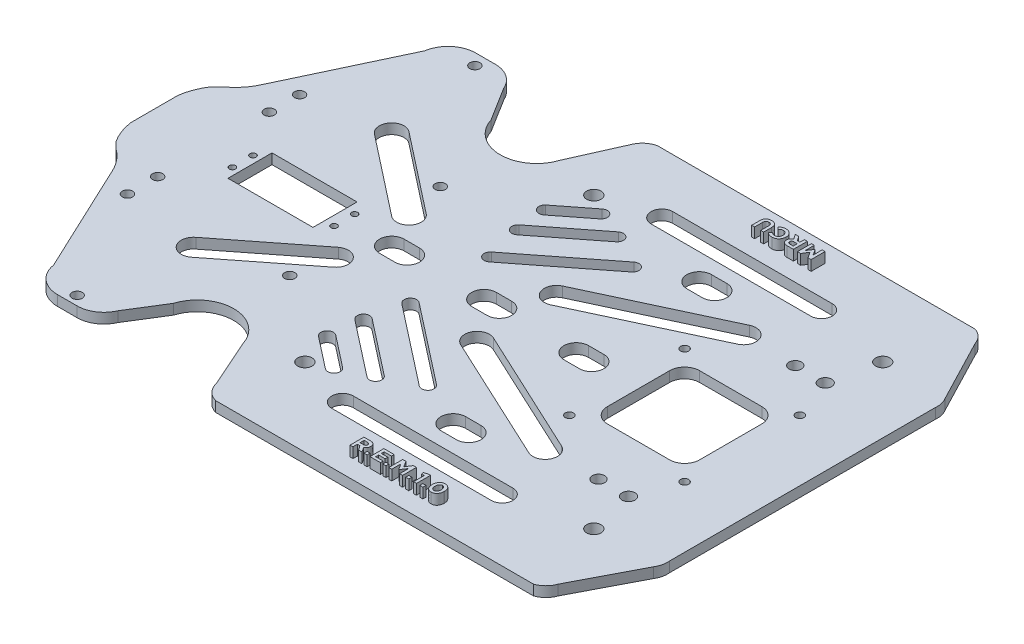
SolidWorks part; units mm, degrees
ref_plane "Front Plane" through (0, 0, 0) normal (0, 0, 1) x (1, 0, 0)
ref_plane "Top Plane" through (0, 0, 0) normal (0, 1, 0) x (1, 0, 0)
ref_plane "Right Plane" through (0, 0, 0) normal (1, 0, 0) x (0, 0, -1)
sketch "Sketch1" plane through (0, 0, 0) normal (0, 1, 0) x (1, 0, 0)
  line L0 (-1500, -0.0781) -> (73500, -0.0781) construction
  line L1 (0, -1000) -> (0, 49000) construction
  line L2 (-150.6518, 26.4257) -> (-153.2975, 23.78)
  line L3 (-157.8453, 11.7876) -> (-157.8453, -10.8775)
  line L4 (-153.2975, -22.8699) -> (-150.6518, -25.5156)
  line L5 (-141.6391, -36.6462) -> (-116.4734, -90.1233)
  line L6 (-103.0506, -101.6219) -> (-93.4928, -101.6219)
  line L7 (-81.4838, -93.7237) -> (-71.0922, -77.0457)
  line L8 (-37.1279, -77.0457) -> (-26.688, -100.4727)
  line L9 (-19.6582, -107.8431) -> (135.4161, -107.8431)
  line L10 (141.4748, -101.8033) -> (157.3462, -71.2851)
  line L11 (158.8522, -64.9974) -> (158.8522, 64.8401)
  line L12 (157.3462, 71.1278) -> (141.4748, 101.646)
  line L13 (135.4161, 107.6858) -> (-19.6582, 107.6858)
  line L14 (-26.688, 101.3828) -> (-37.1279, 77.9558)
  line L15 (-71.0922, 77.9558) -> (-81.4838, 94.6338)
  line L16 (-93.4928, 102.532) -> (-103.0506, 102.532)
  line L17 (-116.4734, 91.0334) -> (-141.6391, 37.5563)
  line L22 (89.8093, 83.5697) -> (11.952, 83.5697)
  line L23 (11.952, 73.0697) -> (89.8093, 73.0697)
  line L24 (-6.436, 67.3784) -> (-21.8022, 55.373)
  line L25 (-18.1047, 50.6541) -> (-2.7385, 62.6595)
  line L26 (7.281, 61.7122) -> (-19.9054, 40.4718)
  line L27 (-16.2114, 35.7438) -> (10.9749, 56.9841)
  line L28 (23.8112, 52.7364) -> (-15.1953, 22.2612)
  line L29 (-11.5014, 17.5331) -> (27.5052, 48.0084)
  line L30 (78.8024, 54.2755) -> (16.5469, 25.2452)
  line L31 (21.6183, 14.3695) -> (83.8738, 43.3998)
  line L32 (48.0667, 54.3972) -> (55.5667, 54.3972)
  line L33 (55.5667, 66.3972) -> (48.0667, 66.3972)
  line L34 (-86.0607, -53.0617) -> (-47.0999, -22.5281)
  line L35 (-54.5037, -13.0876) -> (-93.4646, -43.6212)
  line L36 (48.0667, -5.6028) -> (55.5667, -5.6028)
  line L37 (55.5667, 6.3972) -> (48.0667, 6.3972)
  line L38 (3.0667, -5.6028) -> (10.5667, -5.6028)
  line L39 (10.5667, 6.3972) -> (3.0667, 6.3972)
  line L40 (-41.9333, -5.6028) -> (-34.4333, -5.6028)
  line L41 (-34.4333, 6.3972) -> (-41.9333, 6.3972)
  line L44 (-19.9054, -39.6775) -> (7.281, -60.9178)
  line L45 (10.9749, -56.1898) -> (-16.2114, -34.9494)
  line L46 (-15.1953, -21.4669) -> (23.8112, -51.9421)
  line L47 (27.5052, -47.214) -> (-11.5014, -16.7388)
  line L48 (48.0667, -65.6028) -> (55.5667, -65.6028)
  line L49 (55.5667, -53.6028) -> (48.0667, -53.6028)
  line L50 (11.952, -82.7753) -> (89.8093, -82.7753)
  line L51 (89.8093, -72.2753) -> (11.952, -72.2753)
  line L52 (116.134, 22.8972) -> (85.7494, 22.8972)
  line L53 (123.4417, -14.7951) -> (123.4417, 15.5895)
  line L54 (85.7494, -22.1028) -> (116.134, -22.1028)
  line L55 (78.4417, 15.5895) -> (78.4417, -14.7951)
  line L56 (16.5469, -24.4509) -> (78.8024, -53.4811)
  line L57 (83.8738, -42.6055) -> (21.6183, -13.5752)
  line L58 (-86.0607, 52.9054) -> (-47.0999, 22.3718)
  line L59 (-54.5037, 12.9314) -> (-93.4646, 43.465)
  line L60 (-1118.8056, -0.1232) -> (48881.1944, -0.1232) construction
  line L61 (-118.8056, -1000.1232) -> (-118.8056, 48999.8768) construction
  line L84 (-18.1047, -50.8104) -> (-2.7385, -62.8158)
  line L85 (-6.436, -67.5347) -> (-21.8022, -55.5293)
  line L86 (-89.8594, 22.1796) -> (-89.8594, -22.3358) construction
  line L87 (-69.1094, 10.6107) -> (-110.6094, 10.6107)
  line L88 (-69.1094, -10.8893) -> (-69.1094, 10.6107)
  line L89 (-110.6094, -10.8893) -> (-69.1094, -10.8893)
  line L90 (-110.6094, 10.6107) -> (-110.6094, -10.8893)
  arc A0 (-150.6518, 26.4257) -> (-141.6391, 37.5563) centre (-165.7222, 47.8428) ccw
  arc A1 (-153.2975, 23.78) -> (-157.8453, 11.7876) centre (-131.0414, 8.4816) ccw
  arc A2 (-157.8453, -10.8775) -> (-153.2975, -22.8699) centre (-131.0414, -7.5716) ccw
  arc A3 (-141.6391, -36.6462) -> (-150.6518, -25.5156) centre (-165.7222, -46.9327) ccw
  arc A4 (-116.4734, -90.1233) -> (-103.0506, -101.6219) centre (-103.0506, -88.0381) ccw
  arc A5 (-93.4928, -101.6219) -> (-81.4838, -93.7237) centre (-93.4928, -88.5431) ccw
  arc A6 (-37.1279, -77.0457) -> (-71.0922, -77.0457) centre (-54.11, -82.3517) ccw
  arc A7 (-26.688, -100.4727) -> (-19.6582, -107.8431) centre (-17.0448, -98.3129) ccw
  arc A8 (135.4161, -107.8431) -> (141.4748, -101.8033) centre (132.2552, -98.6136) ccw
  arc A9 (157.3462, -71.2851) -> (158.8522, -64.9974) centre (149.1483, -65.9974) ccw
  arc A10 (158.8522, 64.8401) -> (157.3462, 71.1278) centre (149.1483, 65.8401) ccw
  arc A11 (141.4748, 101.646) -> (135.4161, 107.6858) centre (132.2552, 98.4563) ccw
  arc A12 (-19.6582, 107.6858) -> (-26.688, 101.3828) centre (-17.3775, 98.0705) ccw
  arc A13 (-71.0922, 77.9558) -> (-37.1279, 77.9558) centre (-54.11, 83.2618) ccw
  arc A14 (-81.4838, 94.6338) -> (-93.4928, 102.532) centre (-93.4928, 89.4532) ccw
  arc A15 (-103.0506, 102.532) -> (-116.4734, 91.0334) centre (-103.0506, 88.9482) ccw
  arc A20 (11.952, 83.5697) -> (11.952, 73.0697) centre (11.952, 78.3197) ccw
  arc A21 (89.8093, 73.0697) -> (89.8093, 83.5697) centre (89.8093, 78.3197) ccw
  arc A22 (-21.8022, 55.373) -> (-19.8568, 50.0893) centre (-19.8568, 53.0893) ccw
  arc A23 (-2.7385, 62.6595) -> (-6.436, 67.3784) centre (-4.4906, 65.0947) ccw
  arc A24 (-19.8568, 50.0893) -> (-18.1047, 50.6541) centre (-19.8568, 53.0893) ccw
  arc A25 (-19.9054, 40.4718) -> (-18.0584, 35.1078) centre (-18.0584, 38.1078) ccw
  arc A26 (10.9749, 56.9841) -> (7.281, 61.7122) centre (9.128, 59.3481) ccw
  arc A27 (-18.0584, 35.1078) -> (-16.2114, 35.7438) centre (-18.0584, 38.1078) ccw
  arc A28 (-15.1953, 22.2612) -> (-13.3483, 16.8972) centre (-13.3483, 19.8972) ccw
  arc A29 (27.5052, 48.0084) -> (23.8112, 52.7364) centre (25.6582, 50.3724) ccw
  arc A30 (-13.3483, 16.8972) -> (-11.5014, 17.5331) centre (-13.3483, 19.8972) ccw
  arc A31 (81.3381, 54.8376) -> (78.8024, 54.2755) centre (81.3381, 48.8376) ccw
  arc A32 (83.8738, 43.3998) -> (81.3381, 54.8376) centre (81.3381, 48.8376) ccw
  arc A33 (16.5469, 25.2452) -> (21.6183, 14.3695) centre (19.0826, 19.8074) ccw
  arc A34 (55.5667, 54.3972) -> (55.5667, 66.3972) centre (55.5667, 60.3972) ccw
  arc A35 (48.0667, 66.3972) -> (48.0667, 54.3972) centre (48.0667, 60.3972) ccw
  arc A40 (121.5667, 45.2472) -> (121.5667, 51.5472) centre (121.5667, 48.3972) ccw
  arc A41 (121.5667, 51.5472) -> (121.5667, 45.2472) centre (121.5667, 48.3972) ccw
  arc A42 (106.9417, 45.3972) -> (106.9417, 51.3972) centre (106.9417, 48.3972) ccw
  arc A43 (106.9417, 51.3972) -> (106.9417, 45.3972) centre (106.9417, 48.3972) ccw
  arc A44 (-89.8594, -54.4174) -> (-86.0607, -53.0617) centre (-89.8594, -48.4174) ccw
  arc A45 (-93.4646, -43.6212) -> (-89.8594, -54.4174) centre (-89.8594, -48.4174) ccw
  arc A46 (-47.0999, -22.5281) -> (-54.5037, -13.0876) centre (-50.8986, -17.8837) ccw
  arc A47 (55.5667, -5.6028) -> (55.5667, 6.3972) centre (55.5667, 0.3972) ccw
  arc A48 (48.0667, 6.3972) -> (48.0667, -5.6028) centre (48.0667, 0.3972) ccw
  arc A49 (10.5667, -5.6028) -> (10.5667, 6.3972) centre (10.5667, 0.3972) ccw
  arc A50 (3.0667, 6.3972) -> (3.0667, -5.6028) centre (3.0667, 0.3972) ccw
  arc A51 (-34.4333, -5.6028) -> (-34.4333, 6.3972) centre (-34.4333, 0.3972) ccw
  arc A52 (-41.9333, 6.3972) -> (-41.9333, -5.6028) centre (-41.9333, 0.3972) ccw
  arc A56 (-16.2114, -34.9494) -> (-19.9054, -39.6775) centre (-18.0584, -37.3135) ccw
  arc A57 (9.128, -61.5538) -> (10.9749, -56.1898) centre (9.128, -58.5538) ccw
  arc A58 (7.281, -60.9178) -> (9.128, -61.5538) centre (9.128, -58.5538) ccw
  arc A59 (-11.5014, -16.7388) -> (-15.1953, -21.4669) centre (-13.3483, -19.1028) ccw
  arc A60 (25.6582, -52.5781) -> (27.5052, -47.214) centre (25.6582, -49.5781) ccw
  arc A61 (23.8112, -51.9421) -> (25.6582, -52.5781) centre (25.6582, -49.5781) ccw
  arc A62 (55.5667, -65.6028) -> (55.5667, -53.6028) centre (55.5667, -59.6028) ccw
  arc A63 (48.0667, -53.6028) -> (48.0667, -65.6028) centre (48.0667, -59.6028) ccw
  arc A64 (11.952, -72.2753) -> (11.952, -82.7753) centre (11.952, -77.5253) ccw
  arc A65 (89.8093, -82.7753) -> (89.8093, -72.2753) centre (89.8093, -77.5253) ccw
  arc A66 (85.7494, 22.8972) -> (78.4417, 15.5895) centre (85.7494, 15.5895) ccw
  arc A67 (123.4417, 15.5895) -> (116.134, 22.8972) centre (116.134, 15.5895) ccw
  arc A68 (116.134, -22.1028) -> (123.4417, -14.7951) centre (116.134, -14.7951) ccw
  arc A69 (78.4417, -14.7951) -> (85.7494, -22.1028) centre (85.7494, -14.7951) ccw
  arc A70 (78.8024, -53.4811) -> (83.8738, -42.6055) centre (81.3381, -48.0433) ccw
  arc A71 (19.0826, -13.0131) -> (16.5469, -24.4509) centre (19.0826, -19.0131) ccw
  arc A72 (21.6183, -13.5752) -> (19.0826, -13.0131) centre (19.0826, -19.0131) ccw
  arc A77 (106.9417, -50.6028) -> (106.9417, -44.6028) centre (106.9417, -47.6028) ccw
  arc A78 (106.9417, -44.6028) -> (106.9417, -50.6028) centre (106.9417, -47.6028) ccw
  arc A79 (121.5667, -44.4528) -> (121.5667, -50.7528) centre (121.5667, -47.6028) ccw
  arc A80 (121.5667, -50.7528) -> (121.5667, -44.4528) centre (121.5667, -47.6028) ccw
  arc A81 (-47.0999, 22.3718) -> (-54.5037, 12.9314) centre (-50.8986, 17.7275) cw
  arc A82 (-89.8594, 54.2611) -> (-86.0607, 52.9054) centre (-89.8594, 48.2611) cw
  arc A83 (-93.4646, 43.465) -> (-89.8594, 54.2611) centre (-89.8594, 48.2611) cw
  circle A116 centre (126.7854, 71.2518) radius 3.5
  circle A117 centre (126.7854, -69.7482) radius 3.5
  circle A118 centre (-14.2146, -69.7482) radius 3.5
  circle A119 centre (-14.2146, 71.2518) radius 3.5
  circle A120 centre (-55.3171, 37.4327) radius 2.5
  circle A122 centre (-97.9469, -97.1219) radius 2.5
  circle A123 centre (-54.4437, -36.9102) radius 2.5
  circle A125 centre (-128.4699, -27.3281) radius 2.5
  arc A126 (-2.7385, -62.8158) -> (-6.436, -67.5347) centre (-4.4906, -65.251) cw
  arc A127 (-19.8568, -50.2456) -> (-18.1047, -50.8104) centre (-19.8568, -53.2456) cw
  arc A128 (-21.8022, -55.5293) -> (-19.8568, -50.2456) centre (-19.8568, -53.2456) cw
  circle A130 centre (129.0667, 28.5222) radius 2
  circle A131 centre (72.8167, 28.5222) radius 2
  circle A132 centre (72.8167, -27.7278) radius 2
  circle A133 centre (129.0667, -27.7278) radius 2
  circle A134 centre (-128.4699, -42.0681) radius 2.5
  circle A138 centre (-128.4699, 41.9119) radius 2.5
  circle A139 centre (-128.4699, 27.1719) radius 2.5
  circle A140 centre (-114.1594, -5.1643) radius 1.5
  circle A141 centre (-114.1594, 4.8857) radius 1.5
  circle A142 centre (-64.5594, -5.1643) radius 1.5
  circle A143 centre (-64.5594, 4.8857) radius 1.5
  circle A144 centre (-97.9469, 96.9656) radius 2.5
  point P211 (-89.8594, -0.0781)
  point P236 (-89.8594, -0.0781)
  dimension "D2" = 4
  dimension "D3" = 27.25
  dimension "D7" = 14.74
  dimension "D9" = 6.79
  dimension "D16" = 3
  dimension "D17" = 5
  dimension "D4" = 41.5
  dimension "D5" = 20.75
  dimension "D6" = 21.5
  dimension "D8" = 6.7855
  dimension "D10" = 215.529
  dimension "D11" = 107.765
  dimension "D12" = 3.55
  dimension "D13" = 3.55
  dimension "D14" = 4.55
  dimension "D15" = 4.55
  dimension "D18" = 4.5
extrude "Boss-Extrude4" add sketch "Sketch1" along normal blind 5
sketch "Sketch2" plane through (0, 5, 0) normal (0, 1, 0) x (1, 0, 0)
  line L0 (36.1233, -98.8431) -> (76.1233, -98.8431) construction
  line L1 (-218.7723, 0) -> (218.7723, 0) construction
  line L2 (36.1233, 98.8431) -> (76.1233, 98.8431) construction
  line L3 (-19.6582, -107.8431) -> (135.4161, -107.8431) construction
  text T0 "R.E.M.1.0" font "Gotham Bold" height in points 24
  text T1 "<b>MRCU</b>" font "Gotham Bold" height in points 24
  point P6 (0, 0)
  dimension "D1" = 40
  dimension "D2" = 9
extrude "Boss-Extrude5" add sketch "Sketch2" along normal blind 5
